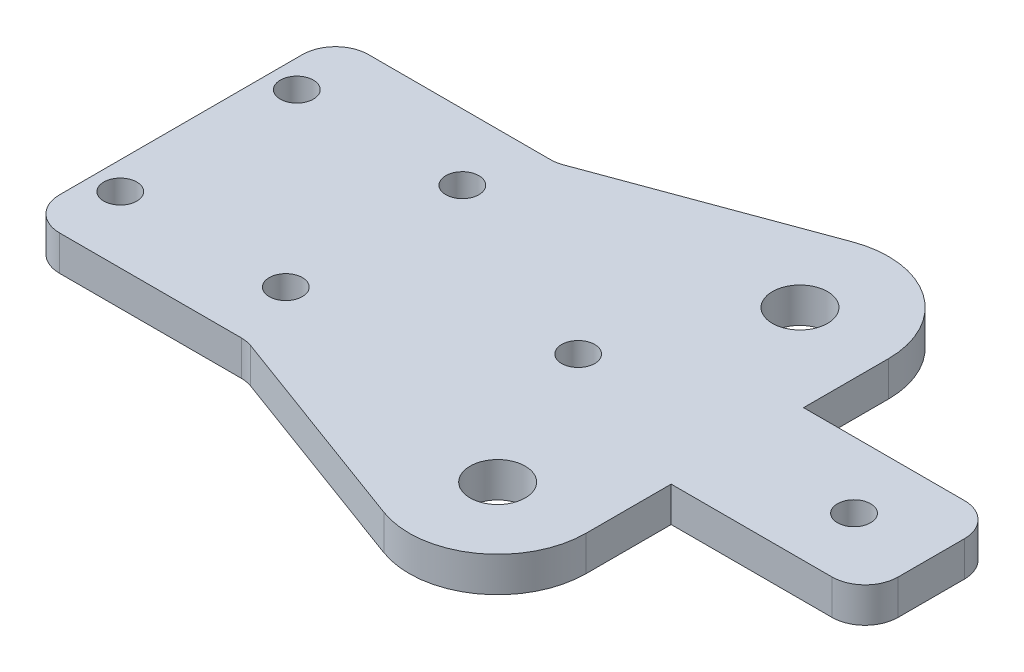
SolidWorks part; units mm, degrees
ref_plane "Front Plane" through (0, 0, 0) normal (0, 0, 1) x (1, 0, 0)
ref_plane "Top Plane" through (0, 0, 0) normal (0, 1, 0) x (1, 0, 0)
ref_plane "Right Plane" through (0, 0, 0) normal (1, 0, 0) x (0, 0, -1)
sketch "Sketch1" plane through (0, 0, 0) normal (0, 1, 0) x (1, 0, 0)
  line L0 (0, -14) -> (0, 14)
  line L1 (0, 14) -> (20, 14)
  line L2 (20, 14) -> (20, -14) construction
  line L3 (20, -14) -> (0, -14)
  line L4 (10, 14) -> (10, -14) construction
  line L5 (0, 0) -> (68, 0) construction
  line L6 (36.2, 14) -> (36.2, -14) construction
  line L7 (2.5, -8) -> (17.5, -8) construction
  line L8 (2.5, -8) -> (2.5, 8) construction
  line L9 (2.5, 8) -> (17.5, 8) construction
  line L10 (17.5, -8) -> (17.5, 8) construction
  line L11 (2.5, -8) -> (17.5, 8) construction
  line L12 (2.5, 8) -> (17.5, -8) construction
  line L13 (20, 14) -> (39.6258, 21.2302)
  line L14 (20, -14) -> (39.6258, -21.2302)
  line L15 (50.425, 13.7) -> (50.425, 6)
  line L16 (68, 6) -> (68, -6)
  line L17 (68, 6) -> (50.425, 6)
  line L18 (68, -6) -> (50.425, -6)
  line L19 (50.425, -6) -> (50.425, -13.7)
  line L20 (22, 14.7368) -> (22, -14.7368) construction
  line L21 (24, 15.4736) -> (24, -15.4736) construction
  line L22 (26, 16.2104) -> (26, -16.2104) construction
  line L23 (22, 14) -> (22, -14) construction
  line L24 (24, 14) -> (24, -14) construction
  line L25 (26, 14) -> (26, -14) construction
  circle A0 centre (2.5, 8) radius 1.5
  circle A1 centre (17.5, 8) radius 1.5
  circle A2 centre (17.5, -8) radius 1.5
  circle A3 centre (2.5, -8) radius 1.5
  circle A4 centre (42.4, 13.7) radius 6.2 construction
  circle A5 centre (42.4, 13.7) radius 2.5
  arc A6 (50.425, 13.7) -> (39.6258, 21.2302) centre (42.4, 13.7) ccw
  circle A7 centre (42.4, -13.7) radius 6.2 construction
  arc A8 (50.425, -13.7) -> (39.6258, -21.2302) centre (42.4, -13.7) cw
  circle A9 centre (42.4, -13.7) radius 2.5
  circle A10 centre (36, 0) radius 1.5
  circle A11 centre (61, 0) radius 1.5
  point P3 (0, 0)
  point P11 (10, 0)
  point P24 (42.4, 7.5)
  point P28 (42.4, -7.5)
  point P32 (68, 0)
  dimension "D5" = 3
  dimension "D7" = 12.4
  dimension "D8" = 5
  dimension "D9" = 16.05
  dimension "D16" = 10
  dimension "D17" = 25
  dimension "D1" = 28
  dimension "D2" = 20
  dimension "D3" = 15
  dimension "D4" = 16
  dimension "D10" = 15
  dimension "D11" = 12
  dimension "D12" = 2
  dimension "D13" = 4
  dimension "D14" = 6
  dimension "D15" = 42
  dimension "D6" = 16.2
extrude "Boss-Extrude1" add sketch "Sketch1" along normal blind 3.175
fillet "Fillet1" radius 3 6 edges at (68, 1.5875, -6) (68, 1.5875, 6) (20, 1.5875, 14) (20, 1.5875, -14) (0, 1.5875, 14) (0, 1.5875, -14)
